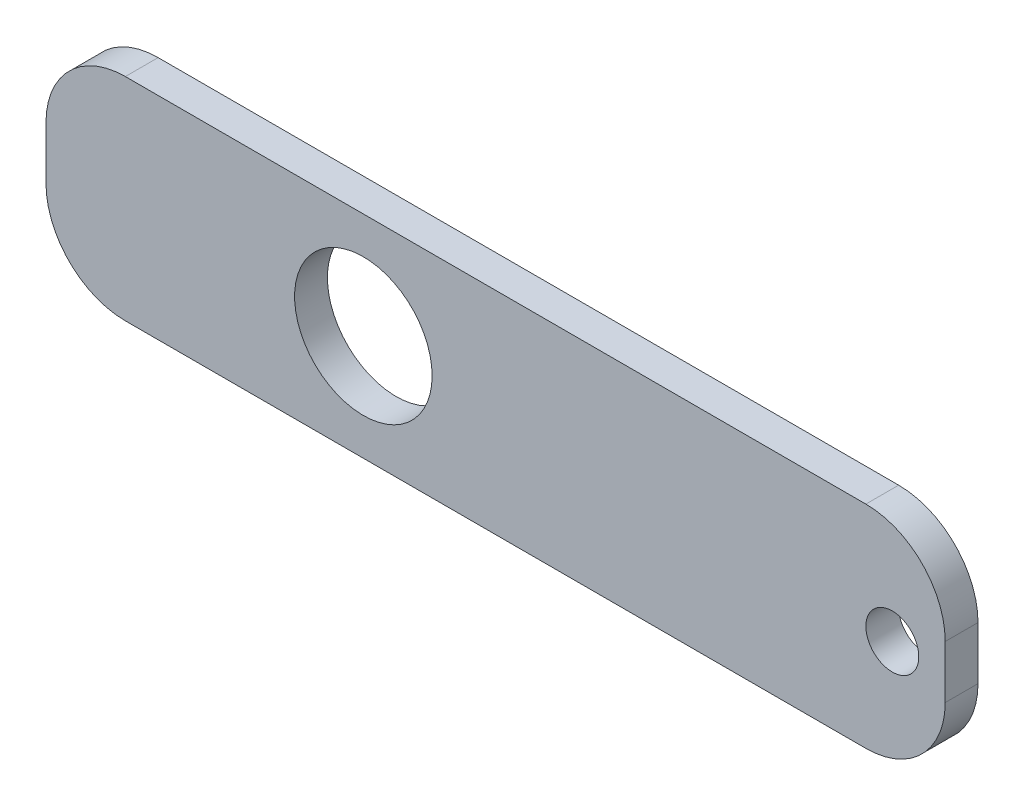
SolidWorks part; units mm, degrees
material "Teak"
ref_plane "Front Plane" through (0, 0, 0) normal (0, 0, 1) x (1, 0, 0)
ref_plane "Top Plane" through (0, 0, 0) normal (0, 1, 0) x (1, 0, 0)
ref_plane "Right Plane" through (0, 0, 0) normal (1, 0, 0) x (0, 0, -1)
sketch "Sketch1" plane through (0, 0, 0) normal (0, 0, 1) x (1, 0, 0)
  line L0 (-47.6194, -10) -> (37.3806, -10)
  line L1 (-47.6194, -10) -> (-47.6194, 10)
  line L2 (37.3806, -10) -> (37.3806, 10)
  line L3 (-47.6194, 10) -> (37.3806, 10)
  line L4 (-47.6194, -10) -> (37.3806, 10) construction
  line L5 (37.3806, -10) -> (-47.6194, 10) construction
  line L6 (-47.6194, 0) -> (37.3806, 0) construction
  line L7 (-5.1194, 10) -> (-5.1194, -10) construction
  line L8 (-17.6194, 0) -> (-17.6194, 10) construction
  circle A1 centre (32.3806, 0) radius 2.5
  circle A4 centre (-17.6194, 0) radius 6.5
  dimension "D3" = 13
  dimension "D8" = 50
  dimension "D1" = 5
  dimension "D2" = 20
  dimension "D4" = 30
  dimension "D7" = 5
extrude "Boss-Extrude1" add sketch "Sketch1" along normal blind 3.1
fillet "Fillet1" radius 7.5 4 edges at (-47.6194, -10, 1.55) (-47.6194, 10, 1.55) (37.3806, -10, 1.55) (37.3806, 10, 1.55)
equation "\"D1@Boss-Extrude1\"=\"thick\""
equation "\"p\"= 20mm"
equation "\"m\"= 1"
equation "\"hole_diam\"= 4mm"
equation "\"len_grip_1\" = 50mm"
equation "\"len_grip_2\" = 50mm"
equation "\"thick\" = 3.1mm"
equation "\"thick2\" = 20mm"
equation "\"wrist_cont_bearing_diam\"=3in"
equation "\"wrist_cont_bearing_thick\"=5/16in"
equation "\"len_forearm\" = 300mm"
equation "\"wrist_bearing_diam\"=3in"
equation "\"len_link\" = 7cm"
equation "\"D1@Sketch1\"=5mm"
equation "\"elbow_cont_bearing_diam\"=10cm"
equation "\"elbow_cont_bearing2_diam\"=7.5cm"
equation "\"small_bearing_outer\"=13mm"
equation "\"servo1_L\"=40.7mm"
equation "\"servo1_W\"=20.5mm"
equation "\"servo1_H\"=43.5mm"
equation "\"servo1_hL\"=49mm"
equation "\"servo1_hW\"=10mm"
equation "\"D7@Sketch1\"=\"D1@Sketch1\""
